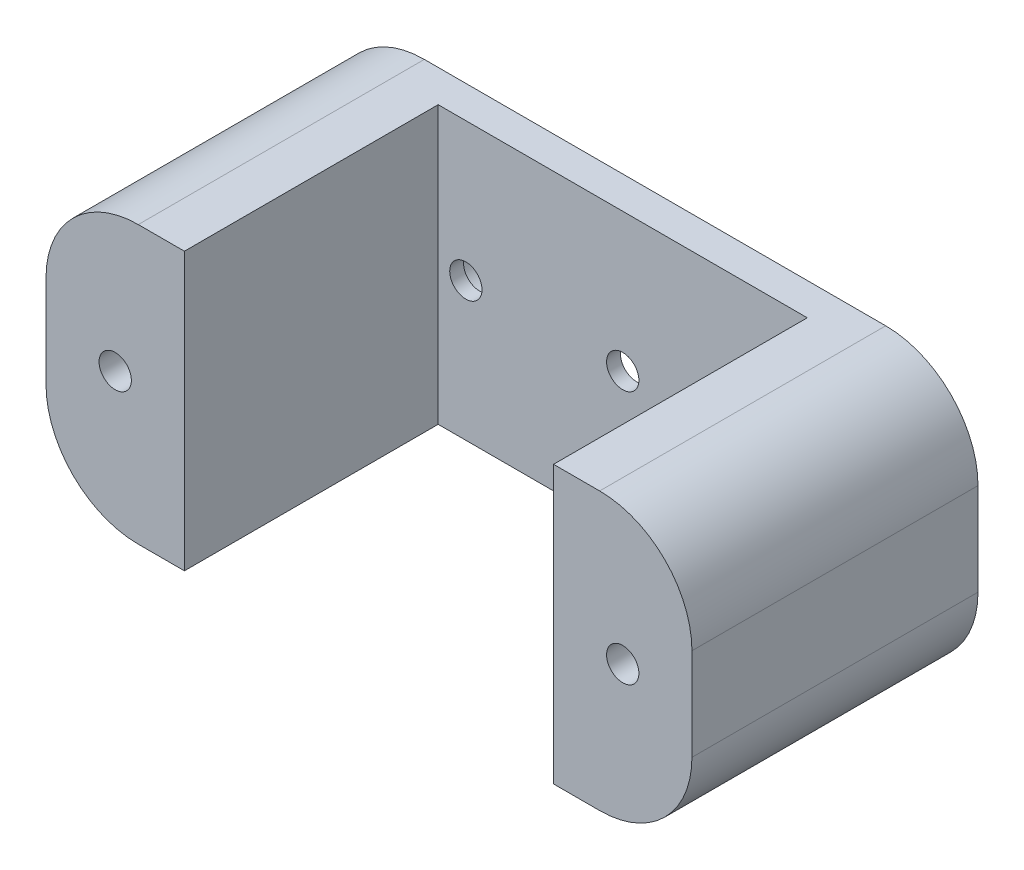
SolidWorks part; units mm, degrees
ref_plane "Front Plane" through (0, 0, 0) normal (0, 0, 1) x (1, 0, 0)
ref_plane "Top Plane" through (0, 0, 0) normal (0, 1, 0) x (1, 0, 0)
ref_plane "Right Plane" through (0, 0, 0) normal (1, 0, 0) x (0, 0, -1)
sketch "Sketch1" plane through (0, 0, 0) normal (0, 0, 1) x (1, 0, 0)
  line L1 (-25, 15) -> (25, 15)
  line L2 (-35, 5) -> (-35, -5)
  line L3 (-25, -15) -> (25, -15)
  line L4 (35, 5) -> (35, -5)
  line L5 (-35, 15) -> (35, -15) construction
  line L6 (-35, -15) -> (35, 15) construction
  arc A0 (25, 15) -> (35, 5) centre (25, 5) cw
  arc A1 (25, -15) -> (35, -5) centre (25, -5) ccw
  arc A2 (-35, -5) -> (-25, -15) centre (-25, -5) ccw
  arc A3 (-25, 15) -> (-35, 5) centre (-25, 5) ccw
  point P0 (0, 0)
  dimension "D3" = 10
  dimension "D1" = 70
  dimension "D2" = 30
extrude "Boss-Extrude1" add sketch "Sketch1" along normal blind 31
sketch "Sketch2" plane through (0, 0, 31) normal (0, 0, 1) x (1, 0, 0)
  line L0 (-25, -15) -> (25, -15) construction
  line L1 (-20, 15) -> (20, 15)
  line L2 (-20, 15) -> (-20, -15)
  line L3 (-20, -15) -> (20, -15)
  line L4 (20, 15) -> (20, -15)
  line L5 (-20, 15) -> (20, -15) construction
  line L6 (-20, -15) -> (20, 15) construction
  point P0 (0, 0)
  dimension "D1" = 40
extrude "Cut-Extrude1" cut sketch "Sketch2" against normal blind 27.5
sketch "Sketch3" plane through (0, 0, 31) normal (0, 0, 1) x (1, 0, 0)
  line L0 (-27.5, 0) -> (27.5, 0) construction
  circle A0 centre (-27.5, 0) radius 1.75
  circle A1 centre (27.5, 0) radius 1.75
  point P3 (0, 0)
  dimension "D2" = 3.5
  dimension "D1" = 55
extrude "Cut-Extrude2" cut sketch "Sketch3" against normal through all
sketch "Sketch4" plane through (0, 0, 0) normal (0, 0, -1) x (-1, 0, 0)
  line L1 (-24.0359, 0) -> (-25.7679, 3)
  line L2 (-25.7679, 3) -> (-29.2321, 3)
  line L3 (-29.2321, 3) -> (-30.9641, 0)
  line L4 (-30.9641, 0) -> (-29.2321, -3)
  line L5 (-29.2321, -3) -> (-25.7679, -3)
  line L6 (-25.7679, -3) -> (-24.0359, 0)
  line L7 (24.0359, 0) -> (25.7679, -3)
  line L8 (25.7679, -3) -> (29.2321, -3)
  line L9 (29.2321, -3) -> (30.9641, 0)
  line L10 (30.9641, 0) -> (29.2321, 3)
  line L11 (29.2321, 3) -> (25.7679, 3)
  line L12 (25.7679, 3) -> (24.0359, 0)
  circle A0 centre (-27.5, 0) radius 3 construction
  circle A1 centre (27.5, 0) radius 3 construction
  point P1 (-31.6197, 0)
  dimension "D1" = 6
extrude "Cut-Extrude3" cut sketch "Sketch4" against normal blind 5
sketch "Sketch5" plane through (0, 0, 0) normal (0, 0, -1) x (-1, 0, 0)
  line L0 (-17, 0) -> (17, 0) construction
  line L1 (-17.4423, 2.4606) -> (-3.3166, 5) construction
  line L2 (-17.4423, -2.4606) -> (-3.3166, -5) construction
  line L3 (3.3166, -5) -> (17.4423, -2.4606) construction
  line L4 (17.4423, 2.4606) -> (3.3166, 5) construction
  line L5 (-3.3166, 5) -> (3.3166, 5) construction
  line L6 (3.3166, 5) -> (3.3166, -5) construction
  line L7 (3.3166, -5) -> (-3.3166, -5) construction
  line L8 (-3.3166, -5) -> (-3.3166, 5) construction
  line L9 (-17.4777, -2.6574) -> (-3.3924, -5.1896)
  line L10 (3.3924, -5.1896) -> (17.4777, -2.6574)
  line L11 (17.4777, 2.6574) -> (3.3924, 5.1896)
  line L12 (-17.4777, 2.6574) -> (-3.3924, 5.1896)
  arc A0 (-3.3166, -5) -> (3.3166, -5) centre (0, 0) ccw construction
  arc A1 (17.4423, -2.4606) -> (17.4423, 2.4606) centre (17, 0) ccw construction
  arc A2 (-17.4423, 2.4606) -> (-17.4423, -2.4606) centre (-17, 0) ccw construction
  arc A3 (3.3166, 5) -> (-3.3166, 5) centre (0, 0) ccw construction
  arc A5 (-3.3924, -5.1896) -> (3.3924, -5.1896) centre (0, 0) ccw
  arc A6 (17.4777, -2.6574) -> (17.4777, 2.6574) centre (17, 0) ccw
  arc A7 (3.3924, 5.1896) -> (-3.3924, 5.1896) centre (0, 0) ccw
  arc A8 (-17.4777, 2.6574) -> (-17.4777, -2.6574) centre (-17, 0) ccw
  point P12 (0, 0)
  point P13 (0, 0)
  dimension "D1" = 12
  dimension "D2" = 5
  dimension "D3" = 34
  dimension "D4" = 10
  dimension "D6" = 0.2
extrude "Cut-Extrude4" cut sketch "Sketch5" against normal blind 2
sketch "Sketch6" plane through (0, 0, 0) normal (0, 0, -1) x (-1, 0, 0)
  circle A0 centre (0, 0) radius 1.75
  circle A1 centre (-17, 0) radius 1.75
  circle A2 centre (17, 0) radius 1.75
  point P8 (-17, 0)
  dimension "D1" = 3.5
extrude "Cut-Extrude5" cut sketch "Sketch6" against normal through all
